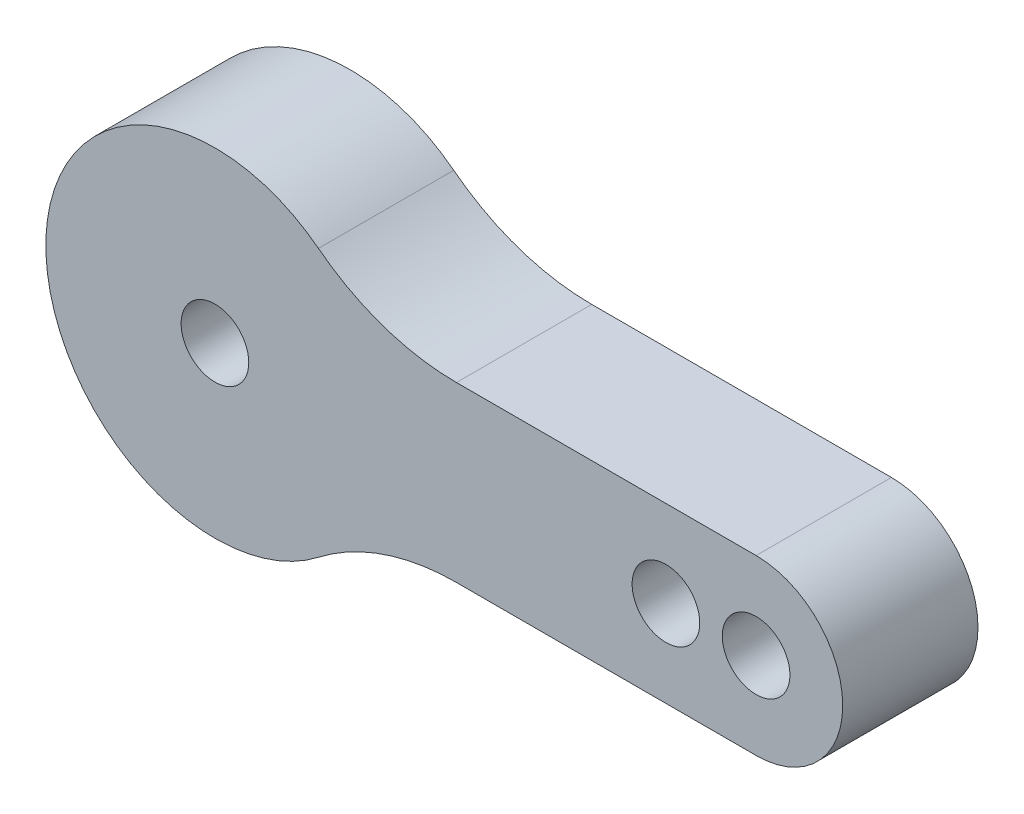
SolidWorks part; units mm, degrees
ref_plane "前视基准面" through (0, 0, 0) normal (0, 0, 1) x (1, 0, 0)
ref_plane "上视基准面" through (0, 0, 0) normal (0, 1, 0) x (1, 0, 0)
ref_plane "右视基准面" through (0, 0, 0) normal (1, 0, 0) x (0, 0, -1)
sketch "草图1" plane through (0, 0, 0) normal (0, 0, 1) x (1, 0, 0)
  line L0 (24, 3.84) -> (10.71, 3.84)
  line L1 (0, 0) -> (24, 0) construction
  line L2 (24, -3.84) -> (10.71, -3.84)
  circle A0 centre (0, 0) radius 1.5
  circle A1 centre (20, 0) radius 1.5
  circle A2 centre (24, 0) radius 1.5
  arc A3 (4.59, 5.9314) -> (4.59, -5.9314) centre (0, 0) ccw
  arc A4 (24, -3.84) -> (24, 3.84) centre (24, 0) ccw
  arc A5 (10.71, -3.84) -> (4.59, -5.9314) centre (10.71, -13.84) ccw
  arc A6 (10.71, 3.84) -> (4.59, 5.9314) centre (10.71, 13.84) cw
  point P13 (6.4424, -3.84)
  point P16 (6.4424, 3.84)
  dimension "D2" = 3
  dimension "D4" = 3
  dimension "D5" = 3
  dimension "D6" = 15
  dimension "D7" = 7.68
  dimension "D8" = 10
  dimension "D1" = 20
  dimension "D3" = 4
extrude "凸台-拉伸2" add sketch "草图1" along normal blind 6
sketch "草图2" plane through (0, 0, 0) normal (0, 0, 1) x (1, 0, 0)
  line L2 (10.71, -3.84) -> (24, -3.84)
  line L3 (24, 3.84) -> (10.71, 3.84)
  line L4 (10.71, -3.84) -> (24, -3.84)
  line L5 (24, 3.84) -> (10.71, 3.84)
  circle A0 centre (0, 0) radius 7.5
  arc A5 (10.71, -3.84) -> (4.59, -5.9314) centre (10.71, -13.84) ccw
  arc A6 (24, -3.84) -> (24, 3.84) centre (24, 0) ccw
  arc A7 (4.59, 5.9314) -> (10.71, 3.84) centre (10.71, 13.84) ccw
  arc A8 (4.59, 5.9314) -> (4.59, -5.9314) centre (0, 0) ccw
  arc A9 (10.71, -3.84) -> (4.59, -5.9314) centre (10.71, -13.84) ccw
  arc A10 (24, -3.84) -> (24, 3.84) centre (24, 0) ccw
  arc A11 (4.59, 5.9314) -> (10.71, 3.84) centre (10.71, 13.84) ccw
  arc A12 (4.59, 5.9314) -> (4.59, -5.9314) centre (0, 0) ccw
  dimension "D1" = 0
